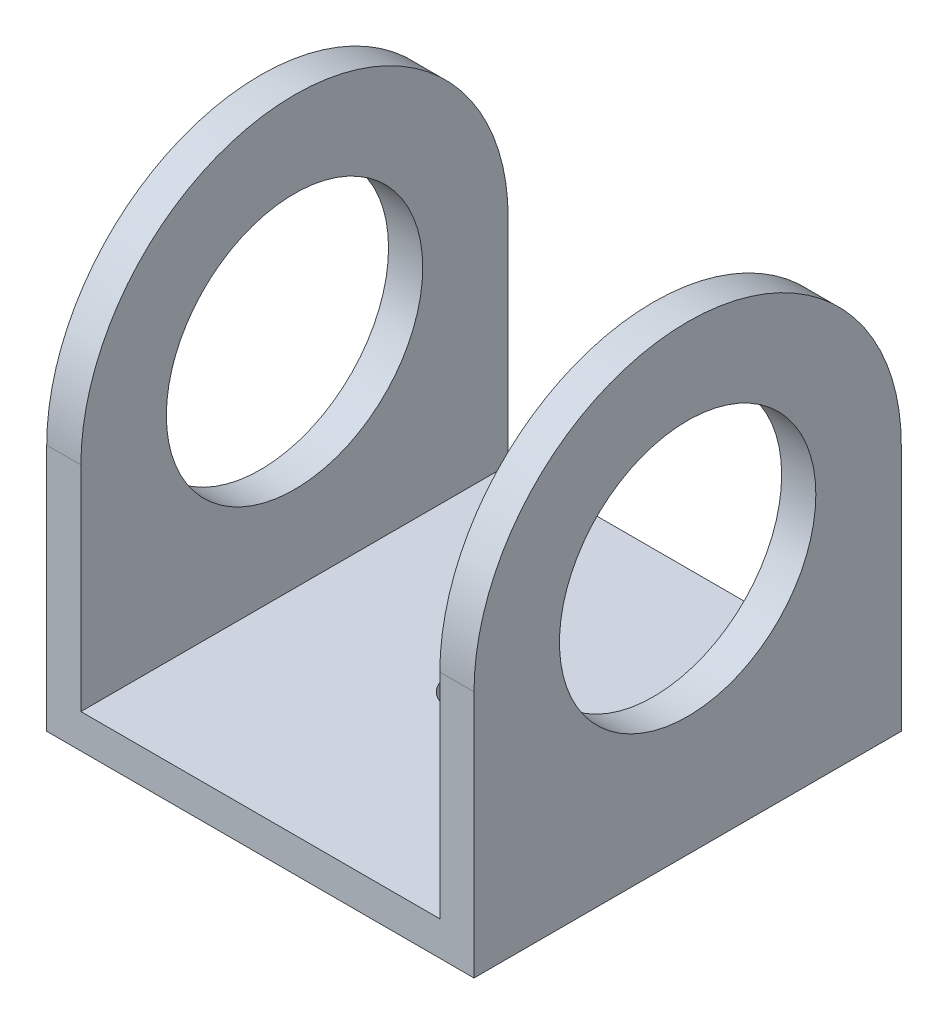
SolidWorks part; units mm, degrees
ref_plane "Front Plane" through (0, 0, 0) normal (0, 0, 1) x (1, 0, 0)
ref_plane "Top Plane" through (0, 0, 0) normal (0, 1, 0) x (1, 0, 0)
ref_plane "Right Plane" through (0, 0, 0) normal (1, 0, 0) x (0, 0, -1)
sketch "Sketch1" plane through (0, 0, 0) normal (0, 1, 0) x (1, 0, 0)
  line L1 (-25.4, -25.4) -> (25.4, -25.4)
  line L2 (-25.4, -25.4) -> (-25.4, 25.4)
  line L3 (-25.4, 25.4) -> (25.4, 25.4)
  line L4 (25.4, -25.4) -> (25.4, 25.4)
  line L5 (-25.4, -25.4) -> (25.4, 25.4) construction
  line L6 (-25.4, 25.4) -> (25.4, -25.4) construction
  circle A0 centre (0, 0) radius 3.175
  point P0 (0, 0)
  dimension "D3" = 6.35
  dimension "D1" = 50.8
  dimension "D2" = 50.8
extrude "Boss-Extrude1" add sketch "Sketch1" along normal blind 4.064
sketch "Sketch2" plane through (0, 4.064, 0) normal (0, 1, 0) x (1, 0, 0)
  line L0 (-25.4, -25.4) -> (25.4, -25.4) construction
  line L1 (-25.4, 25.4) -> (-21.336, 25.4)
  line L2 (-25.4, 25.4) -> (-25.4, -25.4)
  line L3 (-25.4, -25.4) -> (-21.336, -25.4)
  line L4 (-21.336, 25.4) -> (-21.336, -25.4)
  line L6 (25.4, 25.4) -> (21.336, 25.4)
  line L7 (25.4, 25.4) -> (25.4, -25.4)
  line L8 (25.4, -25.4) -> (21.336, -25.4)
  line L9 (21.336, 25.4) -> (21.336, -25.4)
  dimension "D1" = 4.064
  dimension "D2" = 4.064
extrude "Boss-Extrude2" add sketch "Sketch2" along normal blind 50.8
sketch "Sketch3" plane through (25.4, 0, 0) normal (1, 0, 0) x (0, 0, -1)
  line L0 (25.4, 54.864) -> (25.4, 0) construction
  line L1 (-25.4, 0) -> (25.4, 0) construction
  circle A0 centre (0, 29.464) radius 15.24
  dimension "D1" = 30.48
  dimension "D2" = 25.4
  dimension "D3" = 29.464
extrude "Cut-Extrude1" cut sketch "Sketch3" against normal through all
sketch "Sketch4" plane through (-25.4, 0, 0) normal (-1, 0, 0) x (0, 0, 1)
  line L0 (25.4, 0) -> (25.4, 54.864)
  line L1 (25.4, 54.864) -> (-25.4, 54.864)
  line L2 (-25.4, 54.864) -> (-25.4, 0)
  circle A0 centre (0, 29.464) radius 25.4
  line M4 (25.4, 54.864) -> (-25.4, 54.864)
  line M5 (-25.4, 54.864) -> (-25.4, 0)
extrude "Cut-Extrude2" cut sketch "Sketch4" against normal through all contours A0 L1 M5 | A0 L0 M4
